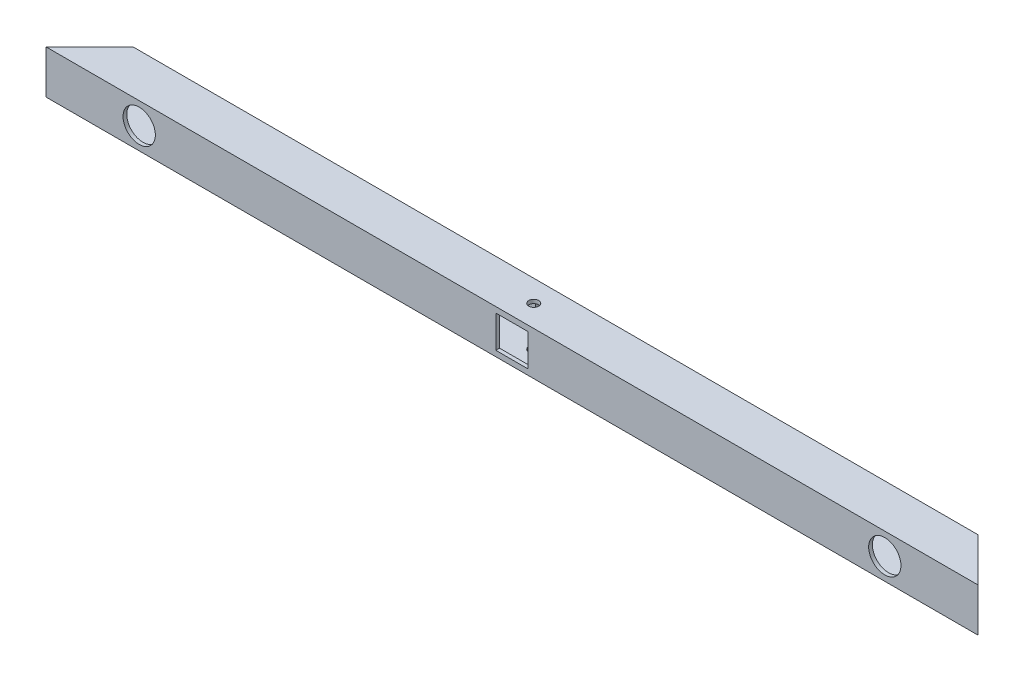
SolidWorks part; units mm, degrees
ref_plane "Front Plane" through (0, 0, 0) normal (0, 0, 1) x (1, 0, 0)
ref_plane "Top Plane" through (0, 0, 0) normal (0, 1, 0) x (1, 0, 0)
ref_plane "Right Plane" through (0, 0, 0) normal (1, 0, 0) x (0, 0, -1)
sketch "Sketch1" plane through (0, 0, 0) normal (0, 1, 0) x (1, 0, 0)
  line L0 (-325, -12.5) -> (-290, 22.5)
  line L1 (-290, 22.5) -> (390, 22.5)
  line L3 (-325, -12.5) -> (425, -12.5)
  line L7 (425, -12.5) -> (390, 22.5)
  dimension "D1" = 750
  dimension "D2" = 45
  dimension "D3" = 45
  dimension "D4" = 35
extrude "Boss-Extrude1" add sketch "Sketch1" along normal blind 35
shell "Shell1" thickness 3
sketch "Sketch4" plane through (0, 0, 12.5) normal (0, 0, 1) x (1, 0, 0)
  line L0 (-325, 35) -> (-325, 0) construction
  line L1 (425, 35) -> (425, 0) construction
  circle A0 centre (-250, 17.5) radius 13
  circle A1 centre (350, 17.5) radius 13
  dimension "D1" = 26
  dimension "D3" = 26
  dimension "D2" = 75
  dimension "D4" = 75
extrude "Cut-Extrude1" cut sketch "Sketch4" against normal blind 49
sketch "Sketch5" plane through (0, 0, -22.5) normal (0, 0, -1) x (-1, 0, 0)
  line L0 (-50, 35) -> (-50, 0) construction
  line L1 (-390, 35) -> (290, 35) construction
  line L2 (-390, 0) -> (290, 0) construction
  line L4 (-63, 30.5) -> (-37, 30.5)
  line L5 (-63, 30.5) -> (-63, 4.5)
  line L6 (-63, 4.5) -> (-37, 4.5)
  line L7 (-37, 30.5) -> (-37, 4.5)
  line L8 (-63, 30.5) -> (-37, 4.5) construction
  line L9 (-63, 4.5) -> (-37, 30.5) construction
  point P6 (-50, 17.5)
  dimension "D1" = 26
  dimension "D2" = 26
extrude "Cut-Extrude2" cut sketch "Sketch5" against normal blind 39
sketch "Sketch6" plane through (0, 35, 0) normal (0, 1, 0) x (1, 0, 0)
  line L0 (-325, -12.5) -> (425, -12.5) construction
  circle A0 centre (50, 5) radius 4
  dimension "D1" = 8
  dimension "D2" = 17.5
extrude "Cut-Extrude3" cut sketch "Sketch6" against normal blind 35
